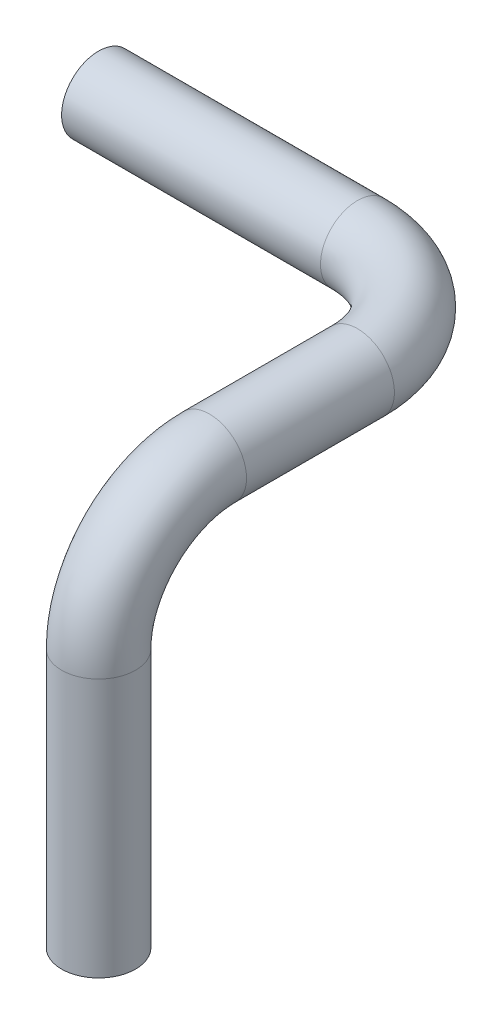
SolidWorks part; units mm, degrees
ref_plane "Front Plane" through (0, 0, 0) normal (0, 0, 1) x (1, 0, 0)
ref_plane "Top Plane" through (0, 0, 0) normal (0, 1, 0) x (1, 0, 0)
ref_plane "Right Plane" through (0, 0, 0) normal (1, 0, 0) x (0, 0, -1)
sketch3d "3DSketch1"
  line L0 (0, 254, 0) -> (177.8, 254, 0)
  line L1 (254, 254, 76.2) -> (254, 254, 177.8)
  line L2 (254, 177.8, 254) -> (254, 0, 254)
  arc A0 (254, 177.8, 254) -> (254, 254, 177.8) centre (254, 177.8, 177.8) ccw
  arc A1 (254, 254, 76.2) -> (177.8, 254, 0) centre (177.8, 254, 76.2) ccw
  point P0 (0, 254, 0)
  point P1 (254, 254, 0)
  point P2 (254, 254, 254)
  point P3 (254, 0, 254)
  point P10 (254, 254, 254)
  point P11 (177.8, 177.8, 177.8)
  point P14 (254, 254, 0)
  point P15 (177.8, 330.2, 76.2)
  dimension "D1" = 76.2
  dimension "D2" = 76.2
sweep "Sweep1" add path "3DSketch1" circular profile diameter 50.8 parameters "D3"=50.8
shell "Shell1" thickness 2.54
